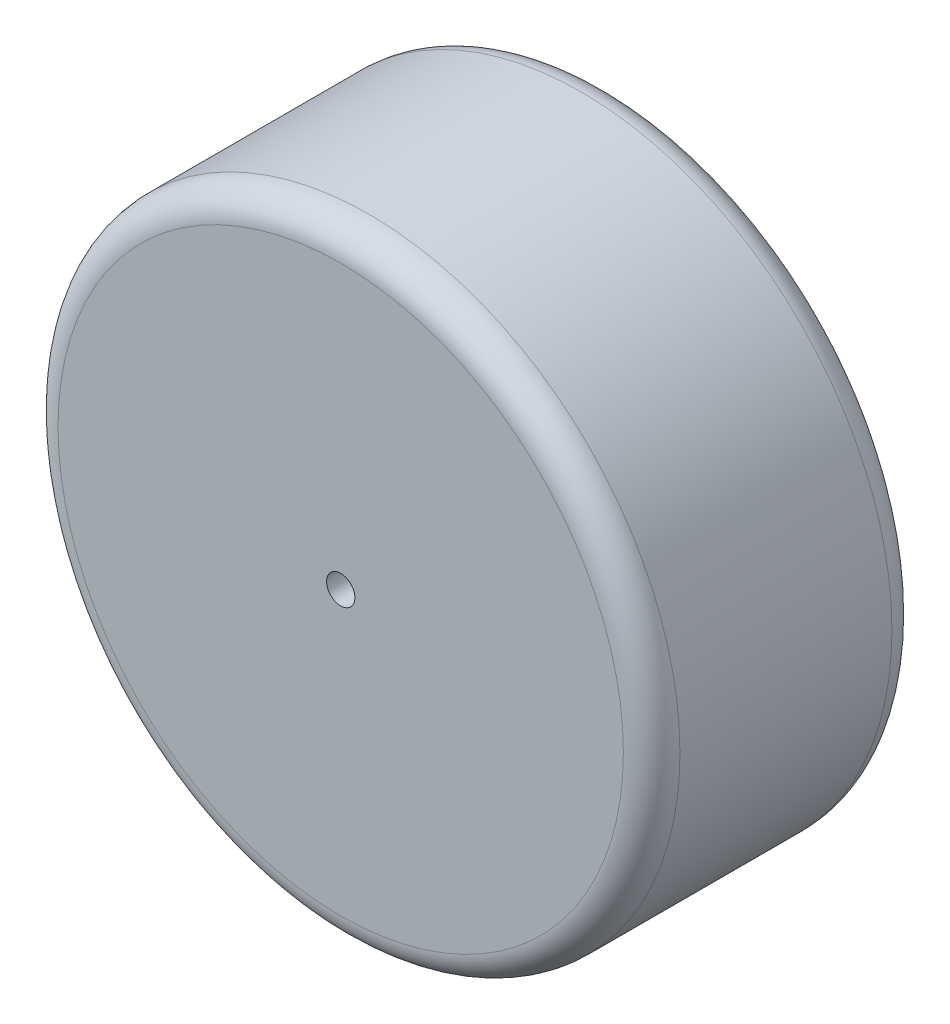
SolidWorks part; units mm, degrees
ref_plane "Front Plane" through (0, 0, 0) normal (0, 0, 1) x (1, 0, 0)
ref_plane "Top Plane" through (0, 0, 0) normal (0, 1, 0) x (1, 0, 0)
ref_plane "Right Plane" through (0, 0, 0) normal (1, 0, 0) x (0, 0, -1)
sketch "Esquisse1" plane through (0, 0, 0) normal (0, 0, 1) x (1, 0, 0)
  circle A0 centre (0, 0) radius 11
  circle A1 centre (0, 0) radius 0.5
  dimension "D1" = 22
  dimension "D2" = 1
extrude "Boss.-Extru.1" add sketch "Esquisse1" along normal blind 9.5
fillet "Congé1" radius 1 2 edges at (11, 0, 0) (11, 0, 9.5)
